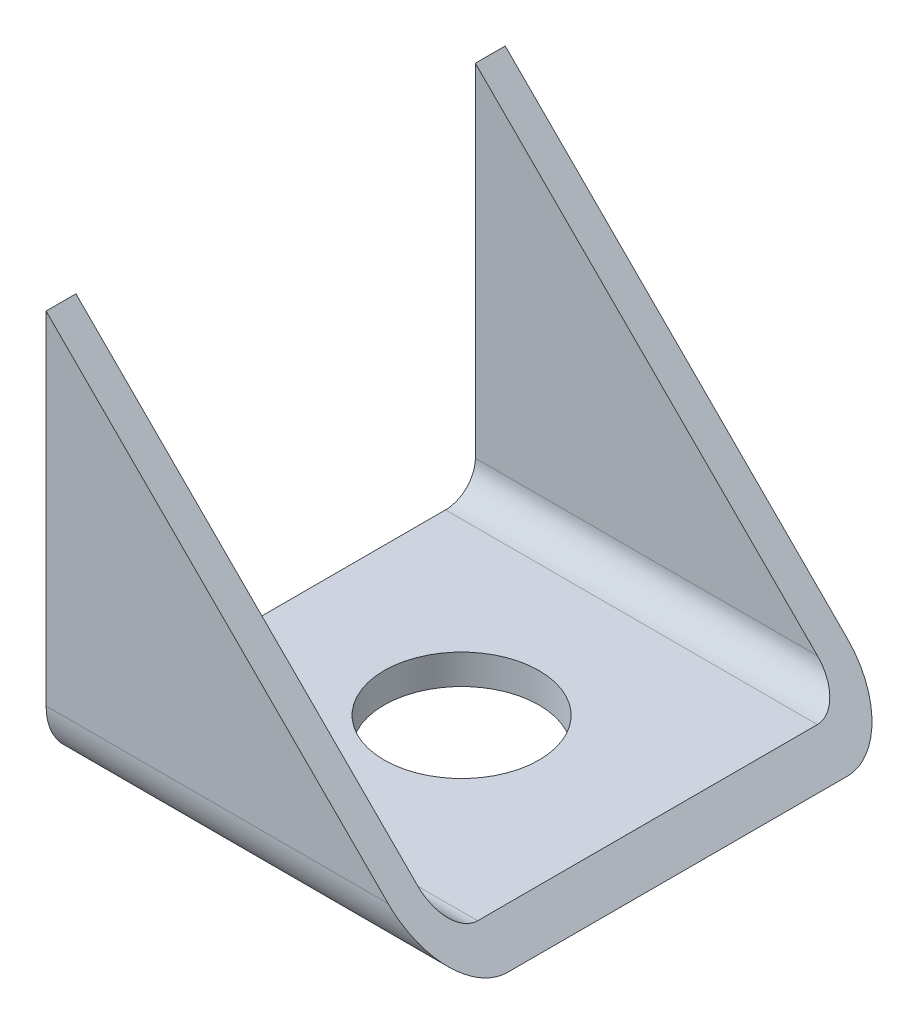
SolidWorks part; units mm, degrees
ref_plane "Front Plane" through (0, 0, 0) normal (0, 0, 1) x (1, 0, 0)
ref_plane "Top Plane" through (0, 0, 0) normal (0, 1, 0) x (1, 0, 0)
ref_plane "Right Plane" through (0, 0, 0) normal (1, 0, 0) x (0, 0, -1)
sketch "Sketch1" plane through (0, 0, 0) normal (0, 0, 1) x (1, 0, 0)
  line L0 (0, 0) -> (35, 0)
  dimension "D1" = 35
other "Tube (square) 40 X 40 X 2.6(1)"
ref_plane "Plane1" through (0, 0, 0) normal (1, 0, 0) x (0, 1, 0)
sketch "Sketch11" plane through (0, 0, 0) normal (1, 0, 0) x (0, 1, 0)
  line L0 (-14.8, -17.4) -> (14.8, -17.4)
  line L1 (-17.4, -14.8) -> (-17.4, 14.8)
  line L2 (14.8, 17.4) -> (-14.8, 17.4)
  line L3 (17.4, 14.8) -> (17.4, -14.8)
  line L4 (-14.8, -20) -> (14.8, -20)
  line L5 (-20, -14.8) -> (-20, 14.8)
  line L6 (14.8, 20) -> (-14.8, 20)
  line L7 (20, 14.8) -> (20, -14.8)
  line L8 (-20, 0) -> (-17.4, 0) construction
  line L9 (-17.4, 0) -> (17.4, 0) construction
  line L10 (17.4, 0) -> (20, 0) construction
  line L12 (0, 20) -> (0, 17.4) construction
  line L13 (0, 17.4) -> (0, -17.4) construction
  line L14 (0, -17.4) -> (0, -20) construction
  arc A0 (20, 14.8) -> (14.8, 20) centre (14.8, 14.8) ccw
  arc A1 (14.8, -20) -> (20, -14.8) centre (14.8, -14.8) ccw
  arc A2 (-20, -14.8) -> (-14.8, -20) centre (-14.8, -14.8) ccw
  arc A3 (-14.8, 20) -> (-20, 14.8) centre (-14.8, 14.8) ccw
  arc A4 (-14.8, 17.4) -> (-17.4, 14.8) centre (-14.8, 14.8) ccw
  arc A5 (17.4, 14.8) -> (14.8, 17.4) centre (14.8, 14.8) ccw
  arc A6 (14.8, -17.4) -> (17.4, -14.8) centre (14.8, -14.8) ccw
  arc A7 (-17.4, -14.8) -> (-14.8, -17.4) centre (-14.8, -14.8) ccw
  point P2 (-20, 20)
  point P33 (-20, -20)
  point P34 (20, -20)
  point P36 (20, 20)
  point P37 (0, 0)
  dimension "D1" = 5.2
  dimension "Thickness" = 2.6
  dimension "V_leg" = 40
  dimension "H_leg" = 40
sketch "Sketch13" plane through (0, 0, 20) normal (0, 0, 1) x (1, 0, 0)
  line L0 (-5, 20) -> (35, -20)
  line L1 (35, -20) -> (35, 20)
  line L2 (35, 20) -> (-5, 20)
  dimension "D1" = 45
extrude "Cut-Extrude1" cut sketch "Sketch13" against normal through all
hole_wizard "M12 Clearance Hole1" positions "Sketch14" profile "Sketch15" hole size "M12" standard "ISO"
sketch "Sketch14" plane through (0, -17.4, 0) normal (0, 1, 0) x (1, 0, 0)
  line L0 (0, 0) -> (32.4, 0) construction
  line L1 (32.4, 14.8) -> (32.4, -14.8) construction
  point P0 (16.2, 0)
sketch "Sketch15" plane through (16.2, -17.4, 0) normal (1, 0, 0) x (0, 0, 1)
  line L0 (0, 0) -> (0, 7.2058)
  line L1 (0, 7.2058) -> (6.75, 3.15)
  line L2 (6.75, 3.15) -> (6.75, 0)
  line L5 (6.75, 0) -> (0, 0)
  line L10 (0, 7.2058) -> (-6.75, 3.15) construction
  line L11 (0, -6.35) -> (0, 107.95) construction
  dimension "Hole Dia." = 13.5
  dimension "Hole Depth" = 3.15
  dimension "Drill Angle" = 118
